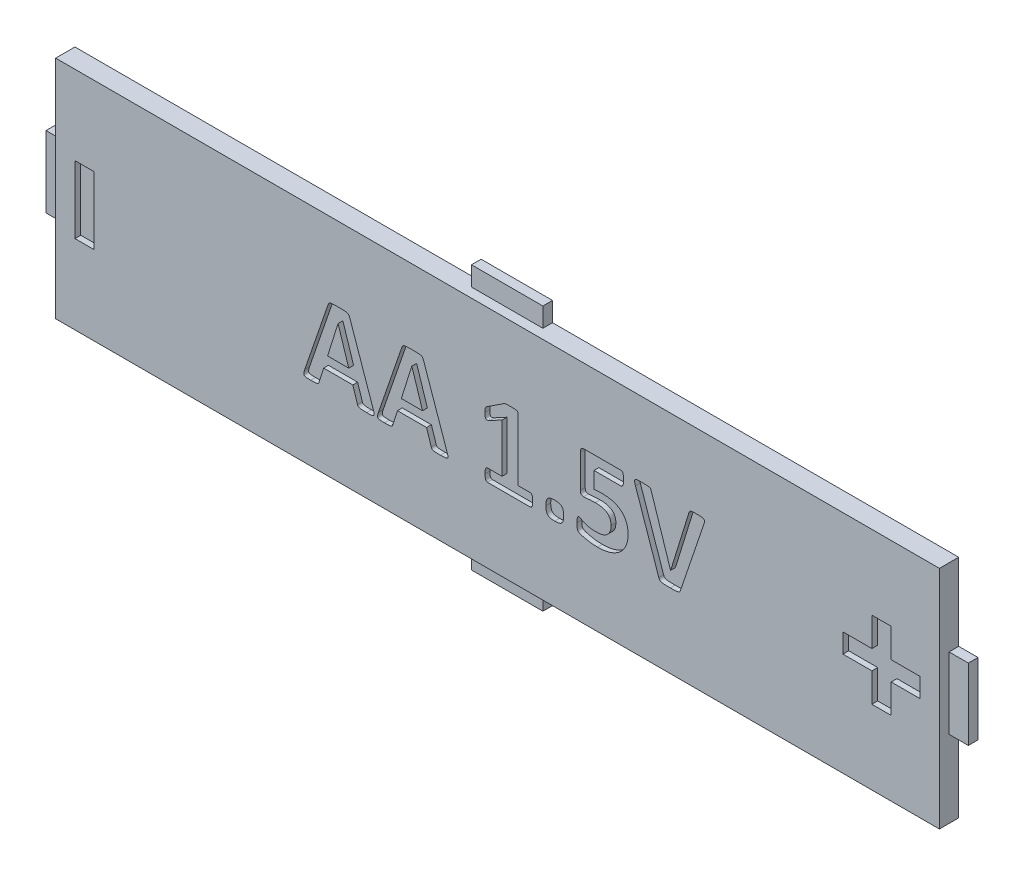
SolidWorks part; units mm, degrees
ref_plane "Front" through (0, 0, 0) normal (0, 0, 1) x (1, 0, 0)
ref_plane "Top" through (0, 0, 0) normal (0, 1, 0) x (1, 0, 0)
ref_plane "Right" through (0, 0, 0) normal (1, 0, 0) x (0, 0, -1)
sketch "Sketch1" plane through (0, 0, 0) normal (0, 0, 1) x (1, 0, 0)
  line L0 (-23.9, 0) -> (23.9, 0) construction
  line L1 (-22.9, -5.85) -> (-1.85, -5.85)
  line L2 (-22.9, -5.85) -> (-22.9, -1.85)
  line L3 (-22.9, 5.85) -> (-1.85, 5.85)
  line L4 (22.9, -5.85) -> (22.9, -1.85)
  line L5 (-22.9, -5.85) -> (22.9, 5.85) construction
  line L6 (-22.9, 5.85) -> (22.9, -5.85) construction
  line L8 (-1.85, 5.85) -> (-1.85, 6.85)
  line L9 (-1.85, 6.85) -> (1.85, 6.85)
  line L10 (1.85, 5.85) -> (1.85, 6.85)
  line L11 (-1.85, -6.85) -> (1.85, -6.85)
  line L12 (1.85, -5.85) -> (1.85, -6.85)
  line L14 (-1.85, -5.85) -> (-1.85, -6.85)
  line L15 (1.85, 5.85) -> (22.9, 5.85)
  line L16 (1.85, -5.85) -> (22.9, -5.85)
  line L17 (0, 6.85) -> (0, -6.85) construction
  line L18 (-23.9, 1.85) -> (-22.9, 1.85)
  line L19 (-23.9, 1.85) -> (-23.9, -1.85)
  line L20 (-23.9, -1.85) -> (-22.9, -1.85)
  line L22 (23.9, -1.85) -> (22.9, -1.85)
  line L23 (23.9, 1.85) -> (22.9, 1.85)
  line L24 (23.9, 1.85) -> (23.9, -1.85)
  line L25 (-22.9, 1.85) -> (-22.9, 5.85)
  line L26 (22.9, 1.85) -> (22.9, 5.85)
  point P0 (0, 0)
  point P10 (0, 6.85)
  dimension "D1" = 11.7
  dimension "D2" = 45.8
  dimension "D3" = 1
  dimension "D5" = 3.7
  dimension "D6" = 1
extrude "Boss-Extrude1" add sketch "Sketch1" along normal blind 1
sketch "Sketch2" plane through (0, 0, 1) normal (0, 0, 1) x (1, 0, 0)
  line L0 (-23.9, 0) -> (23.9, 0) construction
  line L3 (-23.9, -2) -> (23.9, -2) construction
  line L4 (-23.9, 1.85) -> (-23.9, -1.85) construction
  line L5 (23.9, -1.85) -> (23.9, 1.85) construction
  text T0 "<b>AA 1.5V</b>" font "Calibri" height 4
  point P3 (0, 0)
  point P6 (0, 0)
  point P9 (0, 0)
  point P10 (0, 0)
  point P13 (0, 0)
  dimension "D1" = 2
extrude "Cut-Extrude1" cut sketch "Sketch2" against normal blind 0.25
sketch "Sketch4" plane through (0, 0, 0) normal (0, 0, -1) x (-1, 0, 0)
  line L0 (-13.9, -1.05) -> (-13.9, 1.05) construction
  line L1 (-12.85, -1.05) -> (-14.95, -1.05)
  line L2 (-12.85, -1.05) -> (-12.85, 1.05)
  line L3 (-12.85, 1.05) -> (-14.95, 1.05)
  line L4 (-14.95, -1.05) -> (-14.95, 1.05)
  line L5 (-23.9, -1.85) -> (-23.9, 1.85) construction
  point P6 (-13.9, 0)
  point P9 (-23.9, 0)
  dimension "D1" = 10
  dimension "D2" = 2.1
  dimension "D3" = 2.1
extrude "Cut-Extrude3" cut sketch "Sketch4" against normal offset from surface (0.5 mm away) 0.5 up to face at (-4.3931, -0.6939, 1)
fillet "Fillet2" radius 0.4 4 edges at (12.85, -1.05, 0.25) (14.95, -1.05, 0.25) (12.85, 1.05, 0.25) (14.95, 1.05, 0.25)
sketch "Sketch6" plane through (0, 0, 1) normal (0, 0, 1) x (1, 0, 0)
  line L0 (-23.9, 0) -> (23.9, 0) construction
  line L1 (-23.9, 1.85) -> (-23.9, -1.85) construction
  line L2 (23.9, -1.85) -> (23.9, 1.85) construction
  line L3 (20.4, 0.5) -> (21.9, 0.5)
  line L9 (-21.9, -1.75) -> (-20.9, -1.75)
  line L10 (19.4, -2) -> (20.4, -2)
  line L11 (19.4, -2) -> (19.4, -0.5)
  line L12 (19.4, 2) -> (20.4, 2)
  line L13 (20.4, -2) -> (20.4, -0.5)
  line L14 (19.4, -2) -> (20.4, 2) construction
  line L15 (19.4, 2) -> (20.4, -2) construction
  line L16 (17.9, -0.5) -> (19.4, -0.5)
  line L17 (17.9, -0.5) -> (17.9, 0.5)
  line L18 (17.9, 0.5) -> (19.4, 0.5)
  line L19 (21.9, -0.5) -> (21.9, 0.5)
  line L20 (17.9, -0.5) -> (21.9, 0.5) construction
  line L21 (17.9, 0.5) -> (21.9, -0.5) construction
  line L22 (19.4, 0.5) -> (19.4, 2)
  line L23 (20.4, -0.5) -> (21.9, -0.5)
  line L24 (20.4, 0.5) -> (20.4, 2)
  line L25 (-21.9, -1.75) -> (-21.9, 1.75)
  line L26 (-21.9, 1.75) -> (-20.9, 1.75)
  line L27 (-20.9, -1.75) -> (-20.9, 1.75)
  line L28 (-21.9, -1.75) -> (-20.9, 1.75) construction
  line L29 (-21.9, 1.75) -> (-20.9, -1.75) construction
  point P0 (19.9, 0)
  point P7 (-21.4, 0)
  point P28 (19.9, 0)
  dimension "D3" = 2
  dimension "D1" = 3.5
  dimension "D2" = 1
  dimension "D5" = 1
  dimension "D6" = 4
  dimension "D7" = 2
extrude "Cut-Extrude4" cut sketch "Sketch6" against normal blind 0.3
sketch "Sketch7" plane through (0, 0, 1) normal (0, 0, 1) x (1, 0, 0)
  line L0 (-23.9, 0) -> (23.9, 0) construction
  line L1 (-23.9, 1.85) -> (-23.9, -1.85) construction
  line L2 (23.9, -1.85) -> (23.9, 1.85) construction
  line L3 (0, 6.85) -> (0, -6.85) construction
  line L4 (1.85, 6.85) -> (-1.85, 6.85) construction
  line L5 (-1.85, -6.85) -> (1.85, -6.85) construction
  line L6 (23.9, 1.85) -> (22.9, 1.85)
  line L7 (-23.9, -1.85) -> (-22.9, -1.85)
  line L8 (-23.9, -1.85) -> (-23.9, 1.85)
  line L9 (-23.9, 1.85) -> (-22.9, 1.85)
  line L10 (-22.9, -1.85) -> (-22.9, 1.85)
  line L11 (22.9, -1.85) -> (22.9, 1.85)
  line L12 (23.9, -1.85) -> (22.9, -1.85)
  line L13 (23.9, -1.85) -> (23.9, 1.85)
  line L14 (-1.85, 5.85) -> (1.85, 5.85)
  line L15 (-1.85, -6.85) -> (1.85, -6.85)
  line L16 (-1.85, -6.85) -> (-1.85, -5.85)
  line L17 (-1.85, -5.85) -> (1.85, -5.85)
  line L18 (1.85, -6.85) -> (1.85, -5.85)
  line L19 (1.85, 6.85) -> (1.85, 5.85)
  line L20 (-1.85, 6.85) -> (1.85, 6.85)
  line L21 (-1.85, 6.85) -> (-1.85, 5.85)
extrude "Cut-Extrude5" cut sketch "Sketch7" against normal blind 0.5
